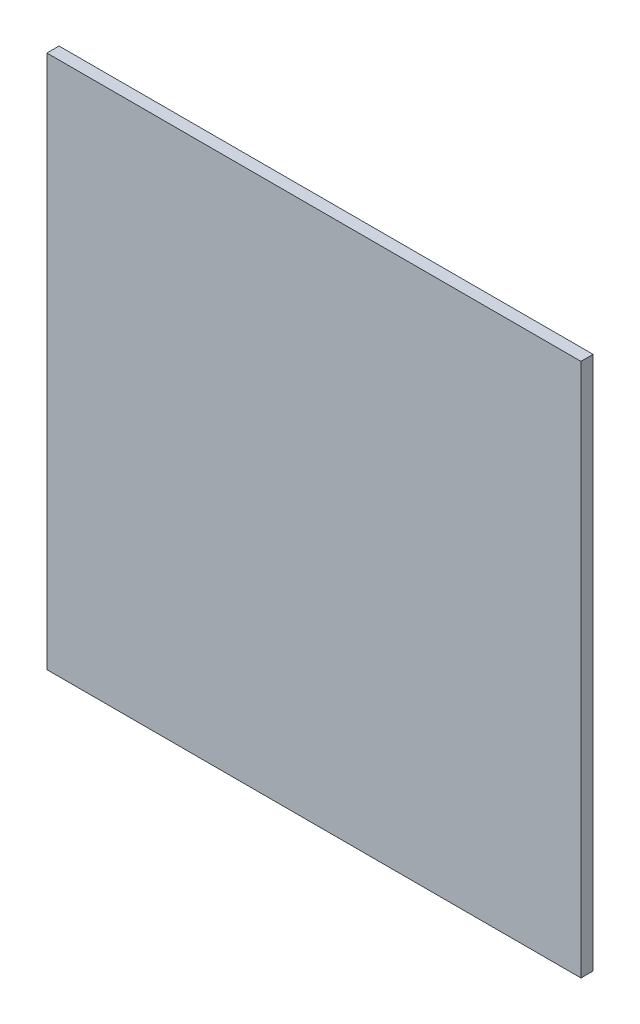
SolidWorks part; units mm, degrees
ref_plane "Front Plane" through (0, 0, 0) normal (0, 0, 1) x (1, 0, 0)
ref_plane "Top Plane" through (0, 0, 0) normal (0, 1, 0) x (1, 0, 0)
ref_plane "Right Plane" through (0, 0, 0) normal (1, 0, 0) x (0, 0, -1)
sketch "Sketch1" plane through (0, 0, 0) normal (0, 0, 1) x (1, 0, 0)
  line L1 (-68.2625, 142.875) -> (71.4375, 142.875)
  line L2 (-68.2625, 142.875) -> (-68.2625, 3.175)
  line L3 (-68.2625, 3.175) -> (71.4375, 3.175)
  line L4 (71.4375, 142.875) -> (71.4375, 3.175)
extrude "Boss-Extrude1" add sketch "Sketch1" along normal blind 3.175 contours L1 L4 L3 L2
